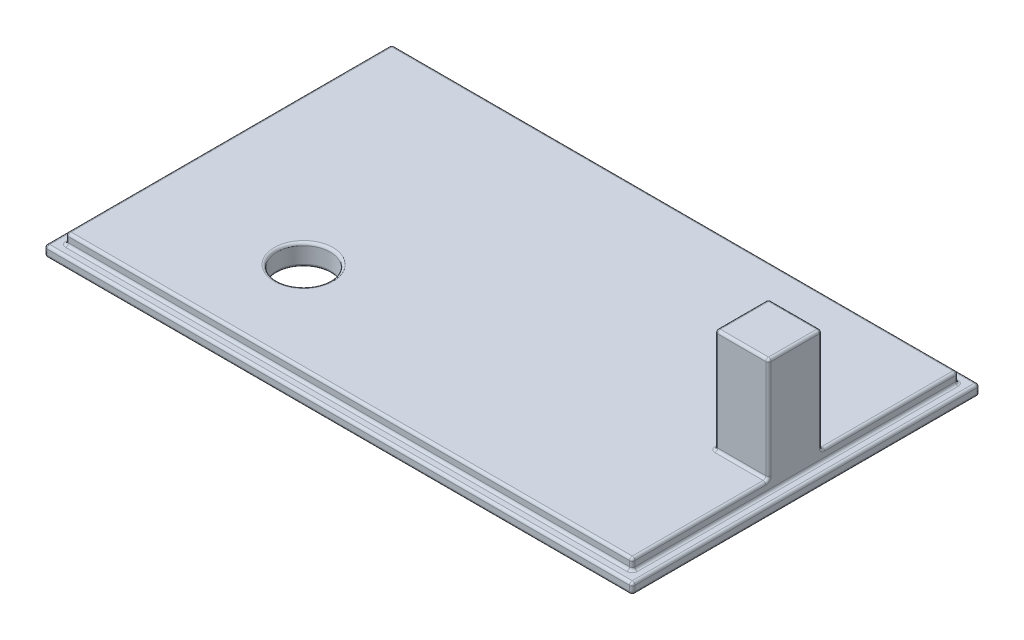
SolidWorks part; units mm, degrees
ref_plane "Front Plane" through (0, 0, 0) normal (0, 0, 1) x (1, 0, 0)
ref_plane "Top Plane" through (0, 0, 0) normal (0, 1, 0) x (1, 0, 0)
ref_plane "Right Plane" through (0, 0, 0) normal (1, 0, 0) x (0, 0, -1)
sketch "Sketch1" plane through (0, 0, 0) normal (0, 1, 0) x (1, 0, 0)
  line L1 (-57.9549, 34.3335) -> (52.0451, 34.3335)
  line L2 (-57.9549, 34.3335) -> (-57.9549, -30.6665)
  line L3 (-57.9549, -30.6665) -> (52.0451, -30.6665)
  line L4 (52.0451, 34.3335) -> (52.0451, -30.6665)
  dimension "D1" = 110
  dimension "D2" = 65
extrude "Boss-Extrude1" add sketch "Sketch1" along normal blind 2
sketch "Sketch2" plane through (0, 2, 0) normal (0, 1, 0) x (1, 0, 0)
  line L0 (-57.9549, 34.3335) -> (-57.9549, -30.6665) construction
  line L1 (-55.9549, 32.3335) -> (50.0451, 32.3335)
  line L2 (-55.9549, 32.3335) -> (-55.9549, -28.6665)
  line L3 (-55.9549, -28.6665) -> (50.0451, -28.6665)
  line L4 (50.0451, 32.3335) -> (50.0451, -28.6665)
  line L5 (-57.9549, -30.6665) -> (52.0451, -30.6665) construction
  line L6 (52.0451, -30.6665) -> (52.0451, 34.3335) construction
  line L7 (52.0451, 34.3335) -> (-57.9549, 34.3335) construction
  dimension "D1" = 2
  dimension "D2" = 2
  dimension "D3" = 2
  dimension "D4" = 2
extrude "Boss-Extrude3" add sketch "Sketch2" along normal blind 2 contours L2 L3 L4 L1
sketch "Sketch6" plane through (0, 4, 0) normal (0, 1, 0) x (1, 0, 0)
  line L0 (50.0451, 32.3335) -> (50.0451, -28.6665) construction
  line L1 (50.0451, 6.8335) -> (40.0451, 6.8335)
  line L2 (50.0451, 6.8335) -> (50.0451, -3.1665)
  line L3 (50.0451, -3.1665) -> (40.0451, -3.1665)
  line L4 (40.0451, 6.8335) -> (40.0451, -3.1665)
  line L8 (-55.9549, -28.6665) -> (50.0451, -28.6665) construction
  dimension "D1" = 10
  dimension "D2" = 10
  dimension "D3" = 25.5
extrude "Boss-Extrude4" add sketch "Sketch6" along normal blind 19.5 contours L3 L4 L1 L2
sketch "Sketch7" plane through (0, 4, 0) normal (0, 1, 0) x (1, 0, 0)
  line L0 (-55.9549, 32.3335) -> (-55.9549, -28.6665) construction
  line L1 (-55.9549, -28.6665) -> (50.0451, -28.6665) construction
  circle A0 centre (-28.4549, -11.6665) radius 5
  dimension "D3" = 10
  dimension "D1" = 27.5
  dimension "D2" = 17
extrude "Cut-Extrude1" cut sketch "Sketch7" against normal through all
fillet "Fillet1" radius 0.5 38 edges at (-57.9549, 0, -1.8335) (50.0451, 4, -19.5835) (50.0451, 4, 15.9165) (-57.9549, 1, -34.3335) (-2.9549, 0, -34.3335) (50.0451, 3, -32.3335) (-2.9549, 4, -32.3335) (50.0451, 13.75, -6.8335) (45.0451, 4, -6.8335) (-55.9549, 3, -32.3335) (-55.9549, 4, -1.8335) (40.0451, 13.75, -6.8335) (40.0451, 4, -1.8335) (52.0451, 1, -34.3335) (52.0451, 0, -1.8335) (40.0451, 23.5, -1.8335) (45.0451, 23.5, -6.8335) (50.0451, 23.5, -1.8335) (40.0451, 13.75, 3.1665) (45.0451, 23.5, 3.1665) (50.0451, 13.75, 3.1665) (45.0451, 4, 3.1665) (-28.4549, 4, 16.6665) (-28.4549, 0, 16.6665) (-57.9549, 1, 30.6665) (52.0451, 1, 30.6665) (-2.9549, 0, 30.6665) (50.0451, 2, -1.8335) (-2.9549, 2, -32.3335) (-55.9549, 2, -1.8335) (-2.9549, 2, -34.3335) (52.0451, 2, -1.8335) (-2.9549, 2, 30.6665) (-57.9549, 2, -1.8335) (-55.9549, 3, 28.6665) (-2.9549, 4, 28.6665) (50.0451, 3, 28.6665) (-2.9549, 2, 28.6665)
equation "\"boxlengthout\"=180"
equation "\"boxwidthout\"= 120"
equation "\"board_arduinoheight\"= 24"
equation "\"boardwidth\"= 60"
equation "\"boardlength\"= 77"
equation "\"batterylength\"= 48"
equation "\"batterywidth\"= 25"
equation "\"batteryheight\"= 15"
equation "\"boxthickenss\"= 2"
equation "\"dividerheight\"=5"
equation "\"D1@Sketch1\"=\"boardlength\"+\"batterywidth\"+3*\"boxthickenss\"+2"
equation "\"D2@Sketch1\"=\"boardwidth\"+\"boxthickenss\"*2+1"
equation "\"D1@Boss-Extrude1\"=\"boxthickenss\""
equation "\"D1@Sketch2\"=\"lid_separation\""
equation "\"lid_separation\"= 2"
equation "\"D2@Sketch2\"=\"lid_separation\""
equation "\"D3@Sketch2\"=\"lid_separation\""
equation "\"lid_depth\"= 2"
equation "\"D1@Boss-Extrude3\"=\"lid_depth\""
equation "\"battery_to_top\"= 19.5"
equation "\"spacer_dim\"= 10"
equation "\"D1@Sketch6\"=\"spacer_dim\""
equation "\"D2@Sketch6\"=\"spacer_dim\""
equation "\"D3@Sketch6\"=(\"RD1@Annotations\"-\"D2@Sketch6\")/2"
equation "\"D1@Boss-Extrude4\"=\"battery_to_top\""
equation "\"short_to_battery\"= 27.5"
equation "\"long_to_battery\"= 17"
equation "\"battery_hole\"= 10"
equation "\"D1@Sketch7\"=\"short_to_battery\""
